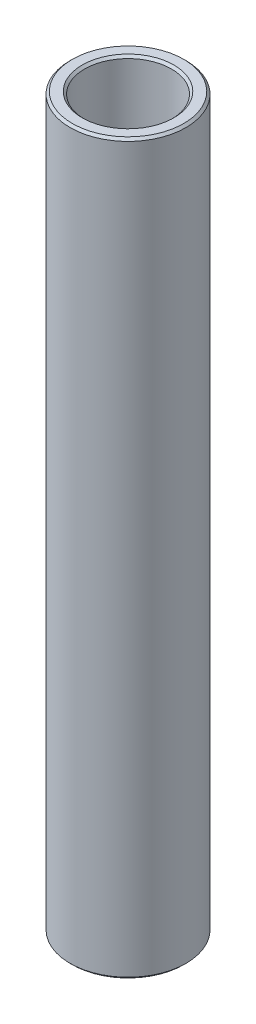
SolidWorks part; units mm, degrees
ref_plane "Front Plane" through (0, 0, 0) normal (0, 0, 1) x (1, 0, 0)
ref_plane "Top Plane" through (0, 0, 0) normal (0, 1, 0) x (1, 0, 0)
ref_plane "Right Plane" through (0, 0, 0) normal (1, 0, 0) x (0, 0, -1)
sketch "Sketch1" plane through (0, 0, 0) normal (0, 0, 1) x (1, 0, 0)
  line L0 (4.7625, 70.6437) -> (4.7625, 150.4156)
  line L1 (4.7625, 150.4156) -> (6.35, 150.4156)
  line L2 (6.35, 150.4156) -> (6.35, 70.6437)
  line L3 (6.35, 70.6437) -> (4.7625, 70.6437)
  line L4 (120.0875, 76.5683) -> (10.0875, 76.5683) construction
  line L6 (0, 61.1187) -> (0, 159.9406) construction
  dimension "D1" = 9.525
  dimension "D2" = 9.525
  dimension "D3" = 12.7
  dimension "D4" = 9.525
revolve "Revolve1" add sketch "Sketch1" angle 360 about L6
chamfer "Chamfer1" distance 0.254 angle 45 4 edges at (6.35, 150.4156, 0) (4.7625, 150.4156, 0) (4.7625, 70.6437, 0) (6.35, 70.6437, 0)
equation "\"D4@Sketch1\"=\"D1@Sketch1\""
